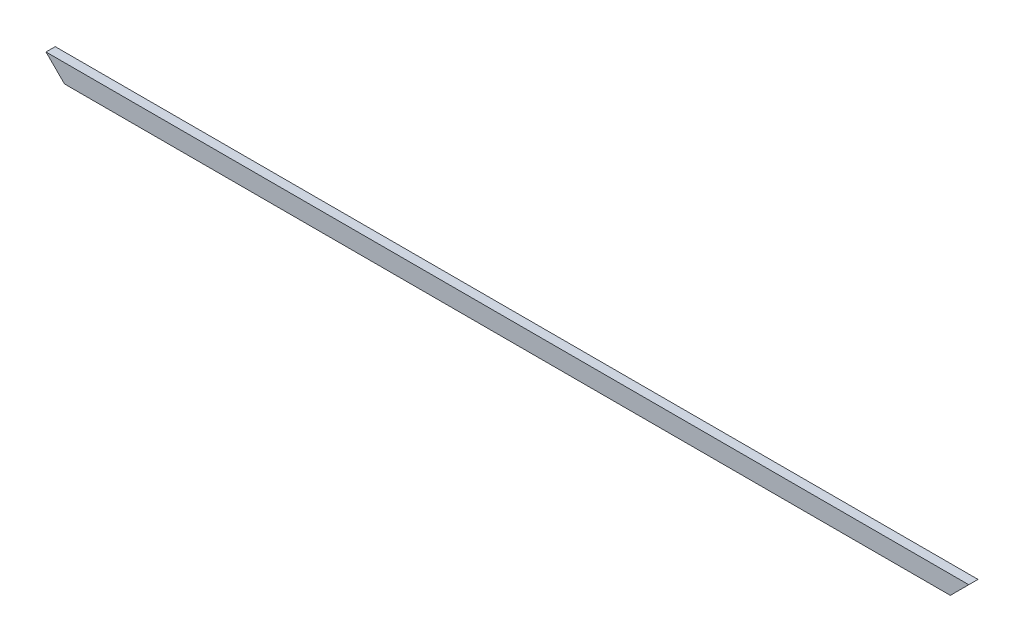
SolidWorks part; units mm, degrees
ref_plane "Plan de face" through (0, 0, 0) normal (0, 0, 1) x (1, 0, 0)
ref_plane "Plan de dessus" through (0, 0, 0) normal (0, 1, 0) x (1, 0, 0)
ref_plane "Plan de droite" through (0, 0, 0) normal (1, 0, 0) x (0, 0, -1)
sketch "Esquisse1" plane through (0, 0, 0) normal (0, 0, 1) x (1, 0, 0)
  line L0 (0, 0) -> (-960, 0)
  line L1 (-960, 0) -> (-980, 20)
  line L2 (-980, 20) -> (20, 20)
  line L3 (20, 20) -> (0, 0)
  dimension "D1" = 20
  dimension "D2" = 135
  dimension "D3" = 1000
extrude "Boss.-Extru.1" add sketch "Esquisse1" along normal blind 10 contours L0 L1 L2 L3
